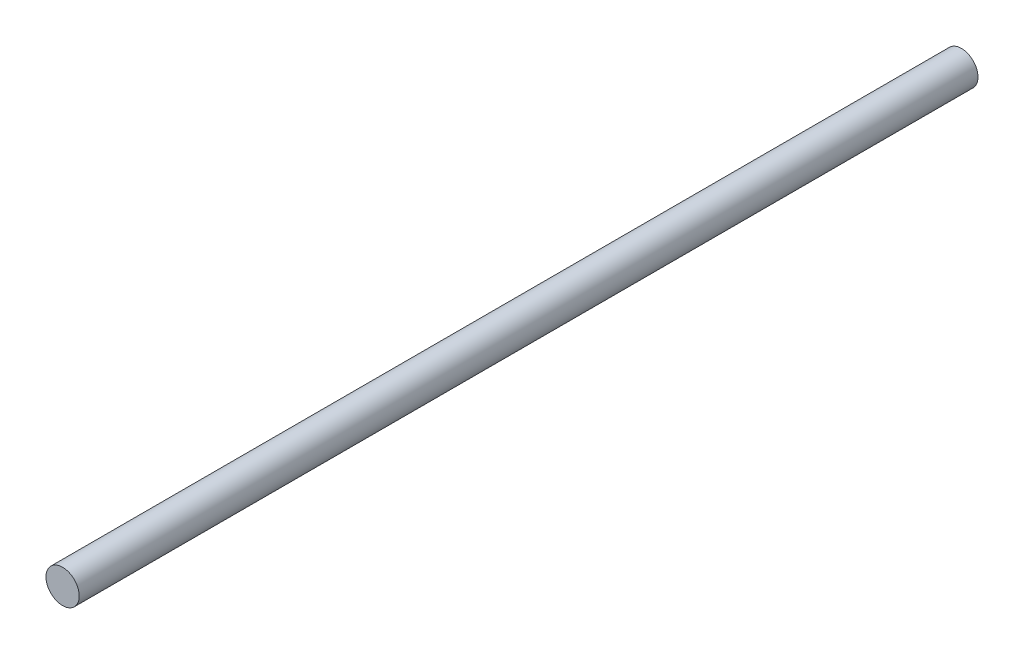
SolidWorks part; units mm, degrees
ref_plane "Plano frontal" through (0, 0, 0) normal (0, 0, 1) x (1, 0, 0)
ref_plane "Plano superior" through (0, 0, 0) normal (0, 1, 0) x (1, 0, 0)
ref_plane "Plano direito" through (0, 0, 0) normal (1, 0, 0) x (0, 0, -1)
sketch "Esboço1" plane through (0, 0, 0) normal (0, 0, 1) x (1, 0, 0)
  circle A0 centre (0, 0) radius 4
  dimension "D1" = 8
extrude "Ressalto-extrusão1" add sketch "Esboço1" along normal mid plane 216.23
